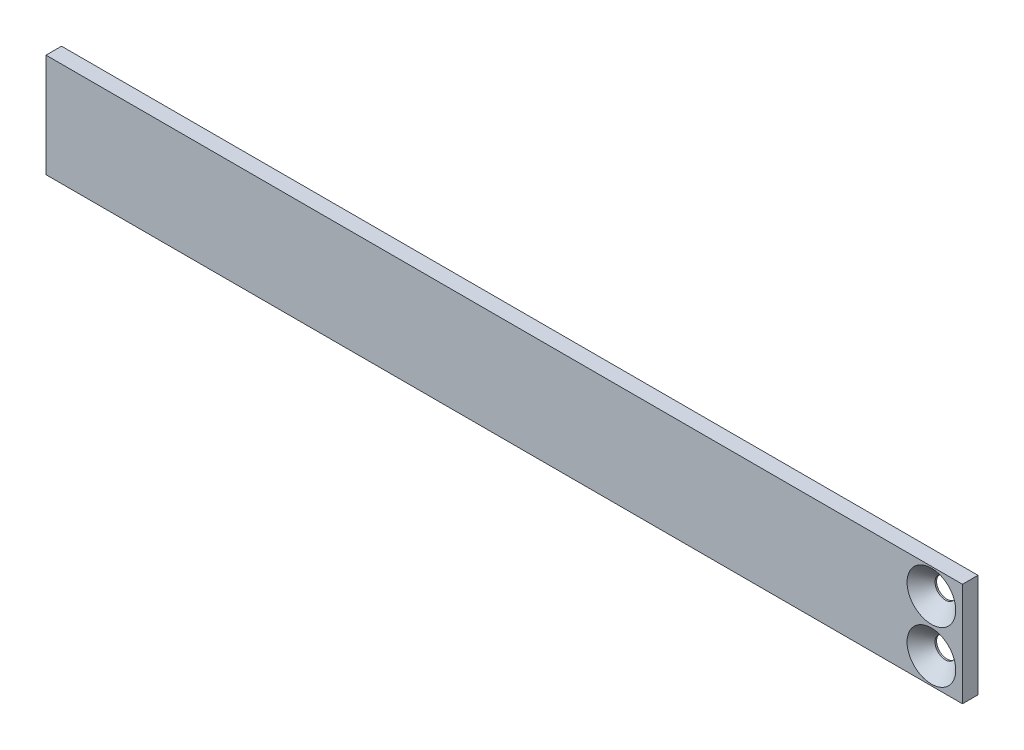
SolidWorks part; units mm, degrees
ref_plane "Ebene vorne" through (0, 0, 0) normal (0, 0, 1) x (1, 0, 0)
ref_plane "Ebene oben" through (0, 0, 0) normal (0, 1, 0) x (1, 0, 0)
ref_plane "Ebene rechts" through (0, 0, 0) normal (1, 0, 0) x (0, 0, -1)
sketch "Skizze1" plane through (0, 0, 0) normal (0, 0, 1) x (1, 0, 0)
  line L1 (0, 0) -> (177, 0)
  line L2 (0, 0) -> (0, 20)
  line L3 (0, 20) -> (177, 20)
  line L4 (177, 0) -> (177, 20)
  dimension "D1" = 177
  dimension "D2" = 20
extrude "Aufsatz-Linear austragen1" add sketch "Skizze1" along normal blind 3
sketch "Skizze3" plane through (0, 0, 3) normal (0, 0, 1) x (1, 0, 0)
  line L0 (0, 0) -> (177, 0) construction
  line L1 (177, 0) -> (177, 20) construction
  circle A0 centre (171, 5) radius 2
  dimension "D1" = 4
  dimension "D2" = 5
  dimension "D3" = 6
extrude "Schnitt-Linear austragen1" cut sketch "Skizze3" against normal blind 8
chamfer "Fase1" distance 2.7 angle 45 1 edges at (173, 5, 3)
sketch "Skizze5" plane through (0, 0, 3) normal (0, 0, 1) x (1, 0, 0)
  line L0 (177, 20) -> (0, 20) construction
  line L1 (177, 0) -> (177, 20) construction
  circle A0 centre (171, 15) radius 2
  dimension "D1" = 4
  dimension "D3" = 6
  dimension "D2" = 5
extrude "Schnitt-Linear austragen2" cut sketch "Skizze5" against normal blind 8
chamfer "Fase2" distance 2.7 angle 45 1 edges at (173, 15, 3)
